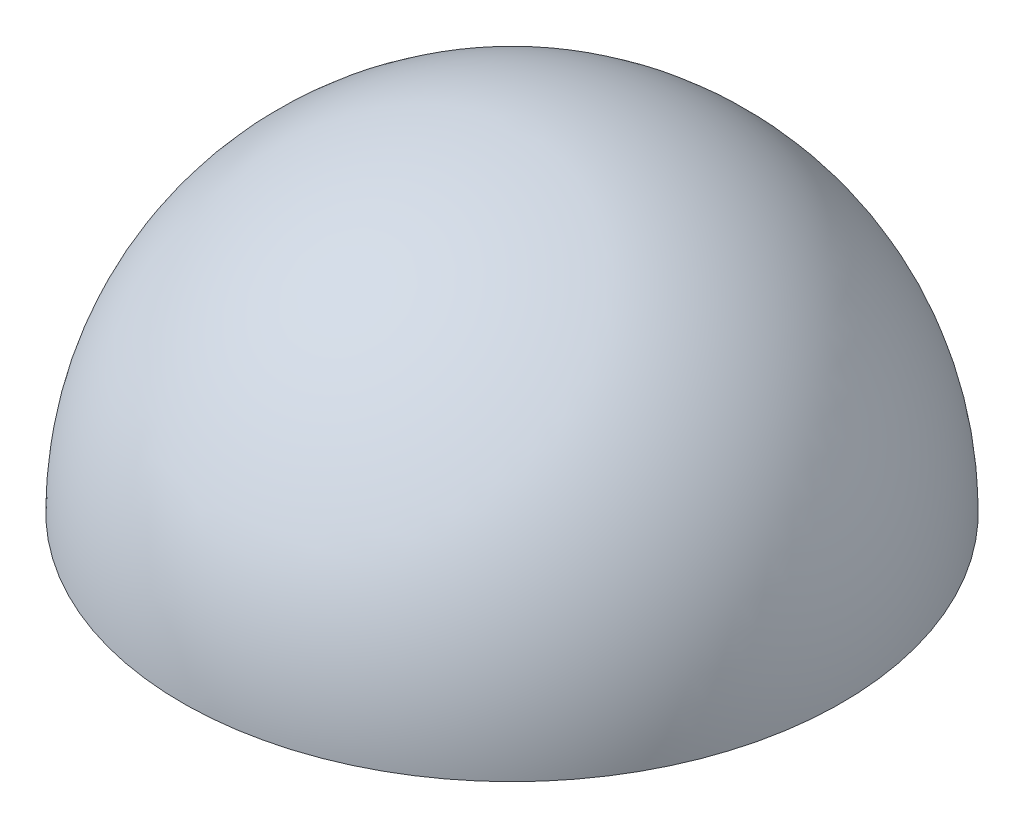
SolidWorks part; units mm, degrees
material "ABS"
ref_plane "Front Plane" through (0, 0, 0) normal (0, 0, 1) x (1, 0, 0)
ref_plane "Top Plane" through (0, 0, 0) normal (0, 1, 0) x (1, 0, 0)
ref_plane "Right Plane" through (0, 0, 0) normal (1, 0, 0) x (0, 0, -1)
sketch "Sketch1" plane through (0, 0, 0) normal (0, 1, 0) x (1, 0, 0)
  line L0 (1.4917, 54.9798) -> (-1.4917, -54.9798)
  arc A0 (-1.4917, -54.9798) -> (1.4917, 54.9798) centre (0, 0) ccw
  dimension "D1" = 110
revolve "Revolve1" add sketch "Sketch1" angle 180 about L0
sketch "Sketch2" plane through (0, 0, 0) normal (0, -1, 0) x (1, 0, 0)
  line L0 (49.9807, 1.3894) -> (-49.9807, -1.3894)
  arc A0 (49.9807, 1.3894) -> (-49.9807, -1.3894) centre (0, 0) ccw
  dimension "D1" = 100
revolve "Cut-Revolve1" cut sketch "Sketch2" angle 360 about L0
sketch "Sketch4" plane through (0, 0, 0) normal (0, -1, 0) x (1, 0, 0)
  circle A0 centre (0, 0) radius 50
  dimension "D1" = 100
extrude "Boss-Extrude1" add sketch "Sketch4" against normal blind 7
sketch "Sketch5" plane through (0, 0, 0) normal (0, -1, 0) x (1, 0, 0)
  circle A0 centre (0, 0) radius 34.5
  dimension "D1" = 69
extrude "Boss-Extrude2" add sketch "Sketch5" along normal blind 12
sketch "Sketch6" plane through (0, -12, 0) normal (0, -1, 0) x (1, 0, 0)
  circle A0 centre (0, 0) radius 39
  dimension "D1" = 78
extrude "Boss-Extrude4" add sketch "Sketch6" against normal blind 4
sketch "Sketch7" plane through (0, -12, 0) normal (0, -1, 0) x (1, 0, 0)
  circle A0 centre (0, 0) radius 30
  dimension "D1" = 60
extrude "Cut-Extrude1" cut sketch "Sketch7" against normal blind 24
sketch "Sketch8" plane through (0, -12, 0) normal (0, -1, 0) x (1, 0, 0)
  line L5 (-10.3528, 38.637) -> (-9.0587, 33.8074)
  line L6 (-28.2843, 28.2843) -> (-24.7487, 24.7487)
  line L9 (-9.0587, -33.8074) -> (-10.3528, -38.637)
  line L10 (-28.2843, -28.2843) -> (-24.7487, -24.7487)
  line L11 (38.637, -10.3528) -> (33.6984, -9.0294)
  line L12 (38.4748, 10.4313) -> (38.637, 10.3528)
  line L13 (38.637, 10.3528) -> (33.8074, 9.0587)
  arc A0 (-28.2843, 28.2843) -> (-28.2843, -28.2843) centre (0, 0) ccw
  arc A1 (-24.7487, 24.7487) -> (-24.7487, -24.7487) centre (0, 0) ccw
  arc A2 (33.8074, 9.0587) -> (-9.0587, 33.8074) centre (0, 0) ccw
  arc A3 (38.637, 10.3528) -> (-10.3528, 38.637) centre (0, 0) ccw
  arc A4 (-9.0587, -33.8074) -> (33.8074, -9.0587) centre (0, 0) ccw
  arc A5 (-10.3528, -38.637) -> (38.637, -10.3528) centre (0, 0) ccw
  circle M4 centre (0, 0) radius 39
  dimension "D1" = 80
  dimension "D2" = 70
  dimension "D3" = 30
  dimension "D4" = 30
  dimension "D5" = 30
  dimension "D6" = 90
  dimension "D7" = 90
  dimension "D8" = 90
  dimension "D9" = 5
extrude "Cut-Extrude2" cut sketch "Sketch8" against normal blind 10 contours A2 L13 L5 M4 | A4 L9 L11 M4 | A1 L6 L10 M4
